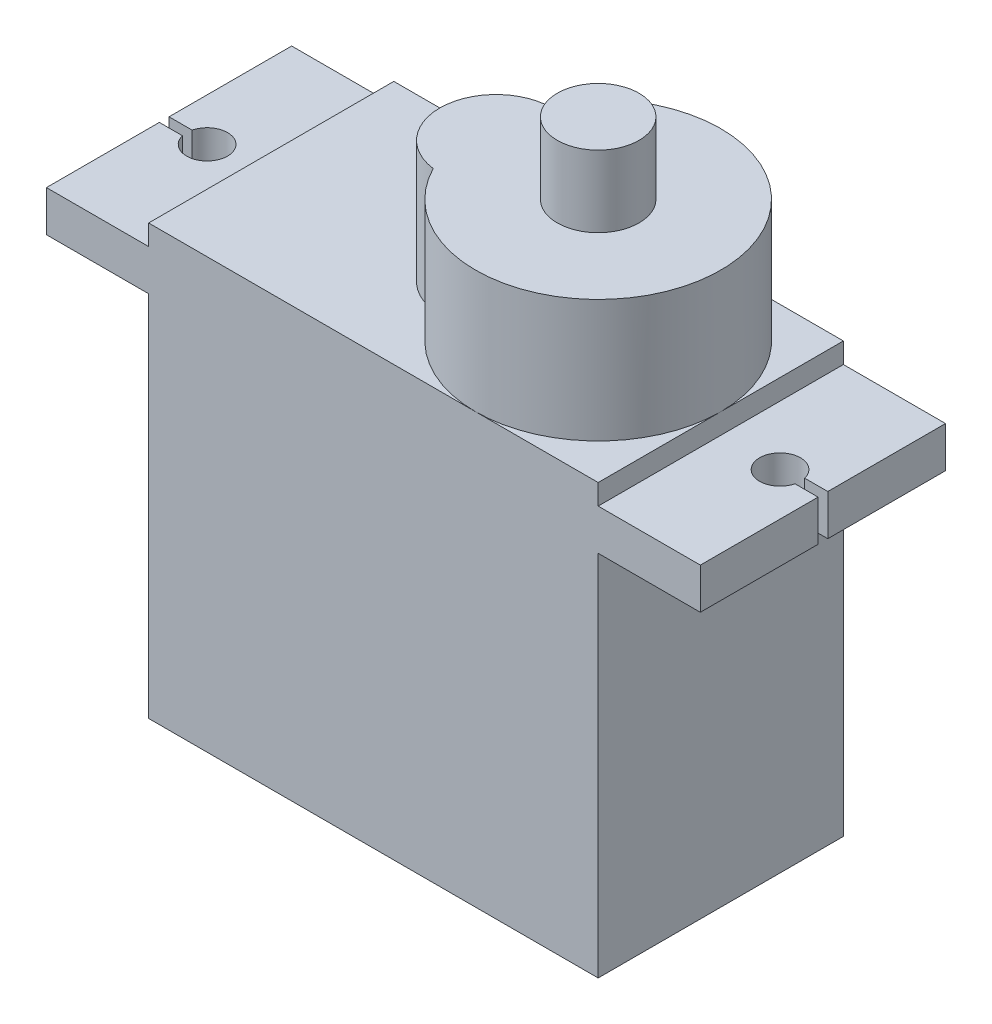
SolidWorks part; units mm, degrees
ref_plane "Ön Düzlem" through (0, 0, 0) normal (0, 0, 1) x (1, 0, 0)
ref_plane "Üst Düzlem" through (0, 0, 0) normal (0, 1, 0) x (1, 0, 0)
ref_plane "Sağ Düzlem" through (0, 0, 0) normal (1, 0, 0) x (0, 0, -1)
sketch "Sketch1" plane through (0, 0, 0) normal (0, 0, 1) x (1, 0, 0)
  line L0 (0, 0) -> (0, 20.1421) construction
  line L6 (-16, 10) -> (-16, 8)
  line L9 (11, 10) -> (11, 11)
  line L10 (16, 10) -> (11, 10)
  line L11 (11, 8) -> (11, -10)
  line L12 (16, 8) -> (11, 8)
  line L13 (-16, 8) -> (-11, 8)
  line L14 (-11, 8) -> (-11, -10)
  line L15 (-16, 10) -> (-11, 10)
  line L16 (-11, 10) -> (-11, 11)
  line L17 (16, 10) -> (16, 8)
  line L18 (-11, 11) -> (11, 11)
  line L19 (-11, -10) -> (11, -10)
  point P0 (0, 0)
  dimension "D1" = 21
  dimension "D2" = 2
  dimension "D3" = 11
  dimension "D4" = 5
  dimension "D5" = 18
  dimension "D6" = 1
extrude "Boss-Extrude1" add sketch "Sketch1" along normal blind 12
sketch "Sketch2" plane through (0, 10, 0) normal (0, 1, 0) x (1, 0, 0)
  line L1 (-16, -12) -> (-16, 0) construction
  line L2 (-16, -6) -> (-14.8718, -6)
  line L3 (-16, -6) -> (-16, -6.4757)
  line L4 (-16, -6.4757) -> (-14.8718, -6.4757)
  line L6 (16, -6.2379) -> (14.8718, -6.2379)
  line L7 (16, -5.7621) -> (16, -6.2379)
  line L8 (16, -5.7621) -> (14.8718, -5.7621)
  arc A0 (-14.8718, -6.4757) -> (-14.8718, -6) centre (-13.9005, -6.2379) ccw
  arc A1 (14.8718, -6.2379) -> (14.8718, -5.7621) centre (13.9005, -6) cw
  point P7 (-16, -6)
  point P16 (21.25, -6)
extrude "Cut-Extrude1" cut sketch "Sketch2" against normal up to next
sketch "Sketch3" plane through (0, 11, 0) normal (0, 1, 0) x (1, 0, 0)
  line L0 (11, -12) -> (11, 0) construction
  arc A0 (-0.3438, -8.7284) -> (-0.3438, -3.2716) centre (5, -6) ccw
  arc A1 (-0.3438, -3.2716) -> (-0.3438, -8.7284) centre (0, -6) ccw
  dimension "D1" = 5.5
  dimension "D2" = 12
  dimension "D3" = 11
  dimension "D4" = 6
extrude "Boss-Extrude2" add sketch "Sketch3" along normal blind 6
sketch "Sketch4" plane through (0, 17, 0) normal (0, 1, 0) x (1, 0, 0)
  circle A0 centre (5, -6) radius 2
  dimension "D1" = 4
extrude "Boss-Extrude3" add sketch "Sketch4" along normal blind 3.5
